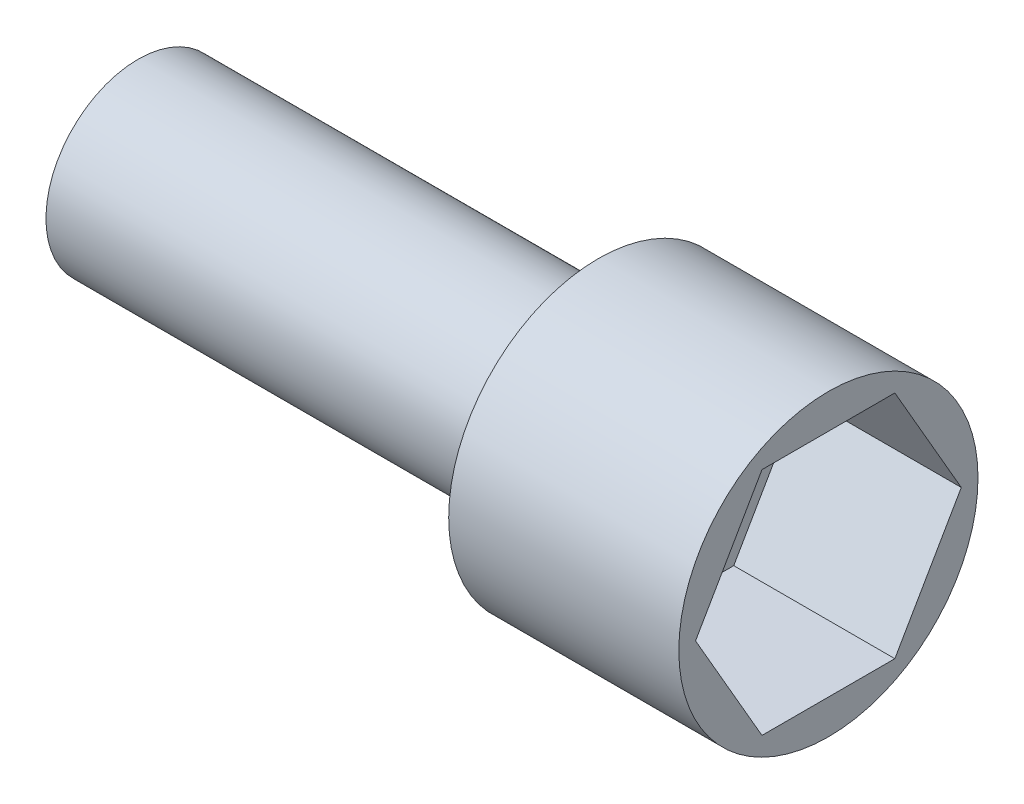
SolidWorks part; units mm, degrees
ref_plane "Front Plane" through (0, 0, 0) normal (0, 0, 1) x (1, 0, 0)
ref_plane "Top Plane" through (0, 0, 0) normal (0, 1, 0) x (1, 0, 0)
ref_plane "Right Plane" through (0, 0, 0) normal (1, 0, 0) x (0, 0, -1)
sketch "Sketch1" plane through (0, 0, 0) normal (0, 0, 1) x (1, 0, 0)
  line L0 (15, 0) -> (-15, 0)
  line L1 (-15, 0) -> (-15, 4)
  line L2 (-15, 4) -> (5, 4)
  line L3 (5, 4) -> (5, 6.5)
  line L4 (5, 6.5) -> (15, 6.5)
  line L5 (15, 6.5) -> (15, 0)
  dimension "D1" = 20
  dimension "D2" = 10
  dimension "D3" = 4
  dimension "D4" = 2.5
  dimension "D5" = 15
revolve "Revolve1" add sketch "Sketch1" angle 360 about L0
sketch "Sketch2" plane through (15, 0, 0) normal (1, 0, 0) x (0, 0, -1)
  line L1 (5.7735, 0) -> (2.8868, 5)
  line L2 (2.8868, 5) -> (-2.8868, 5)
  line L3 (-2.8868, 5) -> (-5.7735, 0)
  line L4 (-5.7735, 0) -> (-2.8868, -5)
  line L5 (-2.8868, -5) -> (2.8868, -5)
  line L6 (2.8868, -5) -> (5.7735, 0)
  circle A0 centre (0, 0) radius 5 construction
  point P1 (0, 0)
  dimension "D1" = 10
extrude "Cut-Extrude1" cut sketch "Sketch2" against normal blind 7
